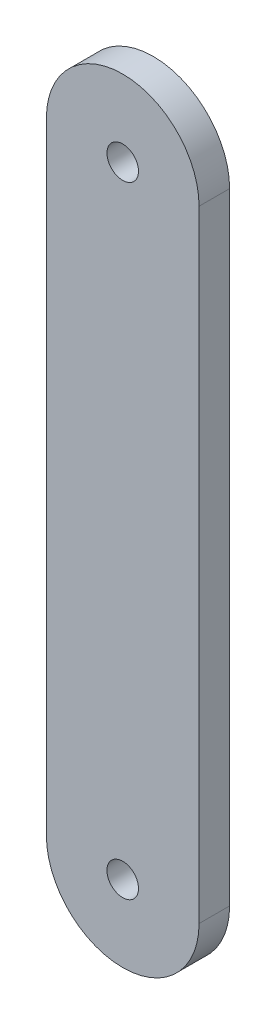
SolidWorks part; units mm, degrees
ref_plane "Alzado" through (0, 0, 0) normal (0, 0, 1) x (1, 0, 0)
ref_plane "Planta" through (0, 0, 0) normal (0, 1, 0) x (1, 0, 0)
ref_plane "Vista lateral" through (0, 0, 0) normal (1, 0, 0) x (0, 0, -1)
sketch "Croquis1" plane through (0, 0, 0) normal (0, 0, 1) x (1, 0, 0)
  line L0 (0, 0) -> (0, 61.03) construction
  line L1 (0, 0) -> (0, 61.03) construction
  line L2 (-7.5, 0) -> (-7.5, 61.03)
  line L3 (7.5, 0) -> (7.5, 61.03)
  circle A0 centre (0, 0) radius 1.55
  circle A1 centre (0, 61.03) radius 1.55
  arc A2 (-7.5, 0) -> (7.5, 0) centre (0, 0) ccw
  arc A3 (7.5, 61.03) -> (-7.5, 61.03) centre (0, 61.03) ccw
  point P7 (0, 30.515)
  point P12 (0, 0)
  point P13 (7.5, 30.515)
  dimension "D2" = 3.1
  dimension "D3" = 3.1
  dimension "D1" = 61.03
  dimension "D4" = 15
extrude "Saliente-Extruir1" add sketch "Croquis1" along normal blind 3
sketch "Croquis2" plane through (0, 0, 3) normal (0, 0, 1) x (1, 0, 0)
  line L0 (0, 61.03) -> (0, 0) construction
